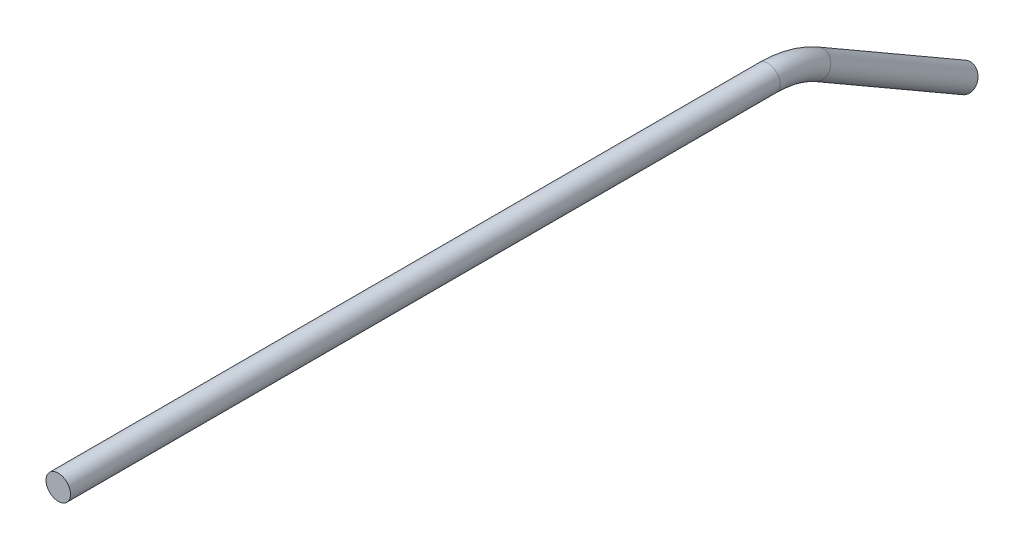
SolidWorks part; units mm, degrees
ref_plane "Front Plane" through (0, 0, 0) normal (0, 0, 1) x (1, 0, 0)
ref_plane "Top Plane" through (0, 0, 0) normal (0, 1, 0) x (1, 0, 0)
ref_plane "Right Plane" through (0, 0, 0) normal (1, 0, 0) x (0, 0, -1)
sketch "Sketch2" plane through (0, 0, 0) normal (0, 0, 1) x (1, 0, 0)
  circle A0 centre (0, 0) radius 3.175
  dimension "D1" = 6.35
sketch "Sketch4" plane through (0, 0, 0) normal (1, 0, 0) x (0, 0, -1)
  line L0 (0, 0) -> (183.6941, 0)
  line L1 (196.3941, -3.403) -> (234.4941, -25.4)
  arc A0 (196.3941, -3.403) -> (183.6941, 0) centre (183.6941, -25.4) ccw
  point P6 (190.5, 0)
  dimension "D4" = 25.4
  dimension "D1" = 190.5
  dimension "D2" = 50.8
  dimension "D3" = 30
sweep "Sweep1" add profiles "Sketch2" path "Sketch4"
